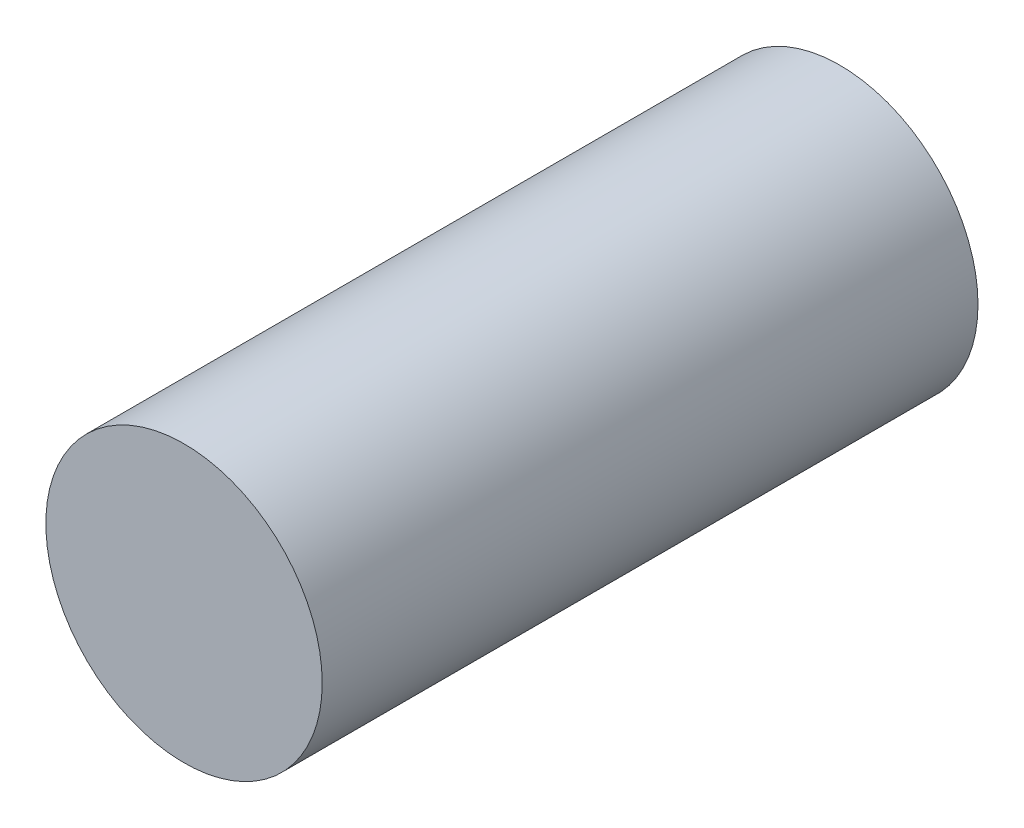
SolidWorks part; units mm, degrees
ref_plane "Front Plane" through (0, 0, 0) normal (0, 0, 1) x (1, 0, 0)
ref_plane "Top Plane" through (0, 0, 0) normal (0, 1, 0) x (1, 0, 0)
ref_plane "Right Plane" through (0, 0, 0) normal (1, 0, 0) x (0, 0, -1)
sketch "Sketch1" plane through (0, 0, 0) normal (0, 0, 1) x (1, 0, 0)
  circle A0 centre (0, 0) radius 2.95
  dimension "D1" = 5.9
extrude "Boss-Extrude1" add sketch "Sketch1" along normal blind 14
